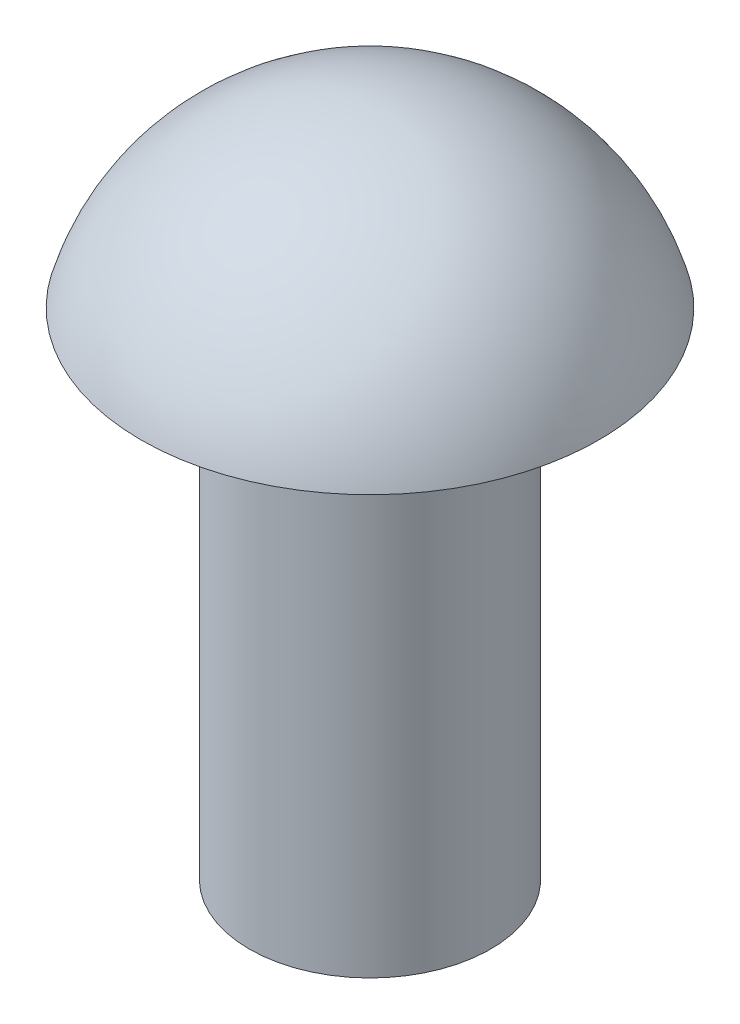
SolidWorks part; units mm, degrees
material "1060 Alloy"
ref_plane "Front Plane" through (0, 0, 0) normal (0, 0, 1) x (1, 0, 0)
ref_plane "Top Plane" through (0, 0, 0) normal (0, 1, 0) x (1, 0, 0)
ref_plane "Right Plane" through (0, 0, 0) normal (1, 0, 0) x (0, 0, -1)
sketch "Sketch1" plane through (0, 0, 0) normal (1, 0, 0) x (0, 0, -1)
  line L0 (0, 0) -> (0, -5.4) construction
  line L1 (0, -5.4) -> (0.975, -5.4)
  line L2 (0.975, -5.4) -> (0.975, -1.4)
  line L3 (0.975, -1.4) -> (1.85, -1.4)
  line L6 (0, 0) -> (0, -5.4)
  arc A0 (1.85, -1.4) -> (0, 0) centre (0, -1.9223) ccw
  dimension "D4" = 1.85
  dimension "D1" = 1.95
  dimension "D2" = 4
  dimension "D3" = 1.4
revolve "Revolve2" add sketch "Sketch1" angle 360 about L0
